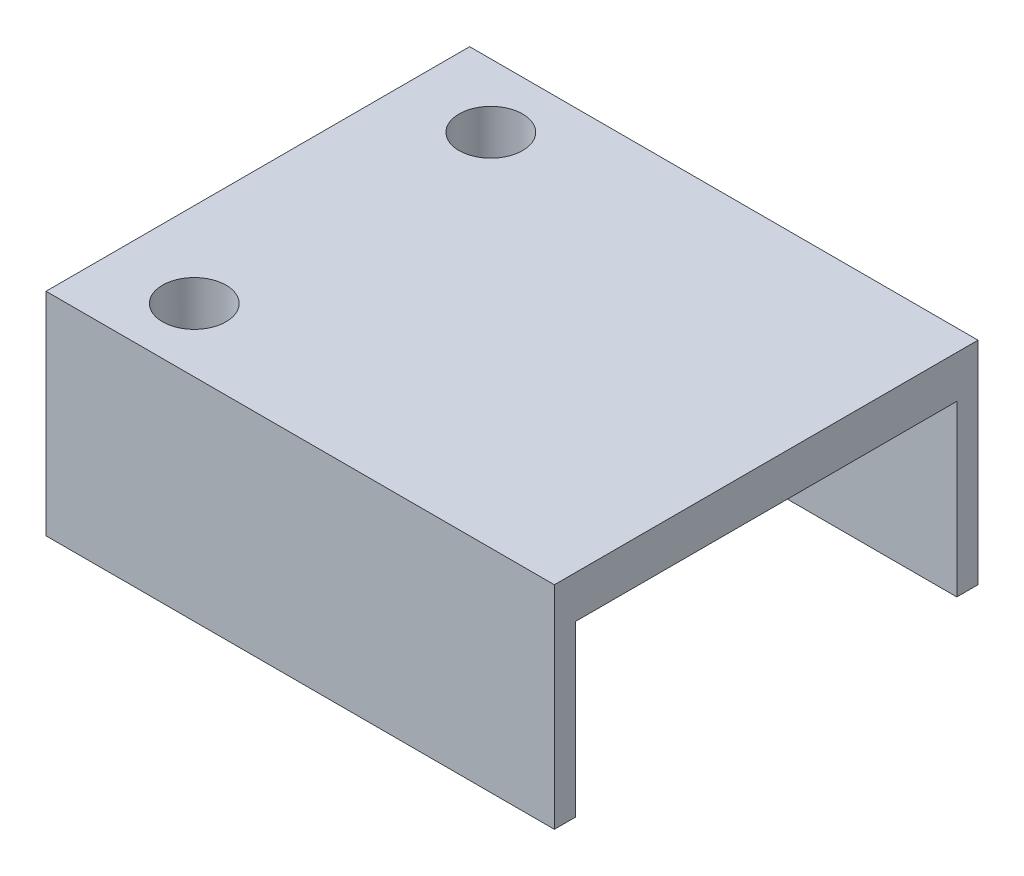
SolidWorks part; units mm, degrees
ref_plane "Plan de face" through (0, 0, 0) normal (0, 0, 1) x (1, 0, 0)
ref_plane "Plan de dessus" through (0, 0, 0) normal (0, 1, 0) x (1, 0, 0)
ref_plane "Plan de droite" through (0, 0, 0) normal (1, 0, 0) x (0, 0, -1)
sketch "Esquisse1" plane through (0, 0, 0) normal (0, 0, 1) x (1, 0, 0)
  line L1 (0, 0) -> (22, 0)
  line L2 (0, 0) -> (0, 10)
  line L3 (0, 10) -> (22, 10)
  line L4 (22, 0) -> (22, 10)
  dimension "D1" = 10
  dimension "D2" = 22
extrude "Boss.-Extru.1" add sketch "Esquisse1" along normal blind 20
sketch "Esquisse2" plane through (0, 10, 0) normal (0, 1, 0) x (1, 0, 0)
  line L0 (0, -10) -> (2.3536, -10) construction
  line L1 (0, -20) -> (0, 0) construction
  circle A0 centre (2, -3) radius 1.5
  circle A1 centre (2, -17) radius 1.5
  dimension "D1" = 2
  dimension "D2" = 2.3536
  dimension "D3" = 7
extrude "Enlèv. mat.-Extru.1" cut sketch "Esquisse2" against normal blind 20
sketch "Esquisse4" plane through (22, 0, 0) normal (1, 0, 0) x (0, 0, -1)
  line L0 (-10, 10) -> (-10, 0) construction
  line L1 (-20, 10) -> (0, 10) construction
  line L2 (-20, 0) -> (0, 0) construction
  line L3 (-1, 8) -> (-1, 0)
  line L5 (-1, 8) -> (-19, 8)
  line L6 (-1, 0) -> (-19, 0)
  line L7 (-19, 8) -> (-19, 0)
  point P11 (-10, 8)
  dimension "D1" = 9
  dimension "D2" = 2
extrude "Enlèv. mat.-Extru.6" cut sketch "Esquisse4" against normal blind 18
sketch "Esquisse5" plane through (0, 0, 0) normal (-1, 0, 0) x (0, 0, 1)
  line L1 (20, 0) -> (0, 0)
  line L2 (20, 0) -> (20, 10)
  line L3 (20, 10) -> (0, 10)
  line L4 (0, 0) -> (0, 10)
extrude "Boss.-Extru.2" add sketch "Esquisse5" along normal blind 2
sketch "Esquisse6" plane through (-2, 0, 0) normal (-1, 0, 0) x (0, 0, 1)
  line L0 (10, 0) -> (10, 7.0904) construction
  line L1 (0, 0) -> (20, 0) construction
  line L4 (14.25, 7.0904) -> (5.75, 7.0904)
  line L5 (14.25, 7.0904) -> (14.25, 0)
  line L6 (14.25, 0) -> (5.75, 0)
  line L7 (5.75, 7.0904) -> (5.75, 0)
  line L8 (14.25, 7.0904) -> (5.75, 0) construction
  line L9 (14.25, 0) -> (5.75, 7.0904) construction
  point P4 (10, 3.5452)
  dimension "D1" = 8.5
extrude "Enlèv. mat.-Extru.7" cut sketch "Esquisse6" against normal blind 8
fillet "Congé1" radius 5 2 edges at (4, 4, 1) (4, 4, 19)
